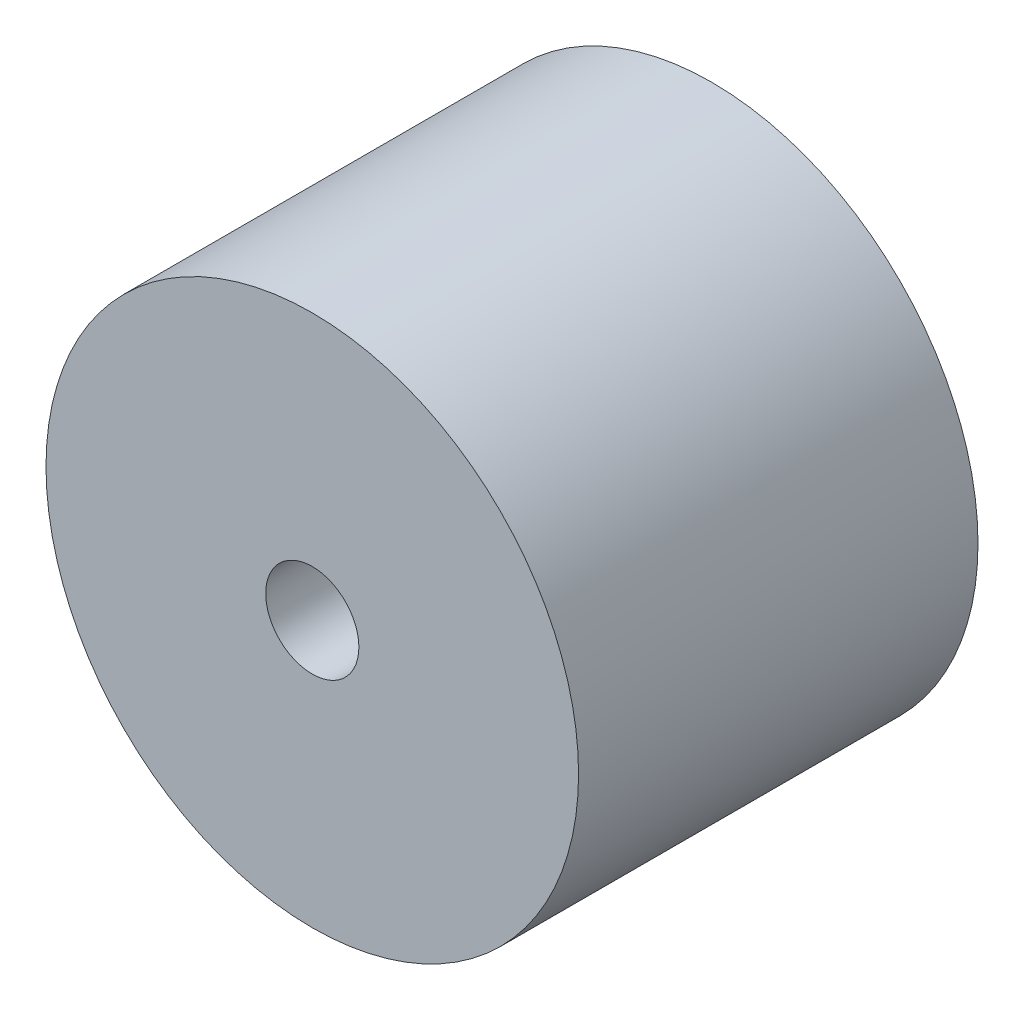
SolidWorks part; units mm, degrees
ref_plane "Front Plane" through (0, 0, 0) normal (0, 0, 1) x (1, 0, 0)
ref_plane "Top Plane" through (0, 0, 0) normal (0, 1, 0) x (1, 0, 0)
ref_plane "Right Plane" through (0, 0, 0) normal (1, 0, 0) x (0, 0, -1)
sketch "Sketch2" plane through (0, 0, 0) normal (0, 0, 1) x (1, 0, 0)
  circle A0 centre (0, 0) radius 10
  circle A1 centre (0, 0) radius 1.75
extrude "Boss-Extrude1" add sketch "Sketch2" along normal blind 15
